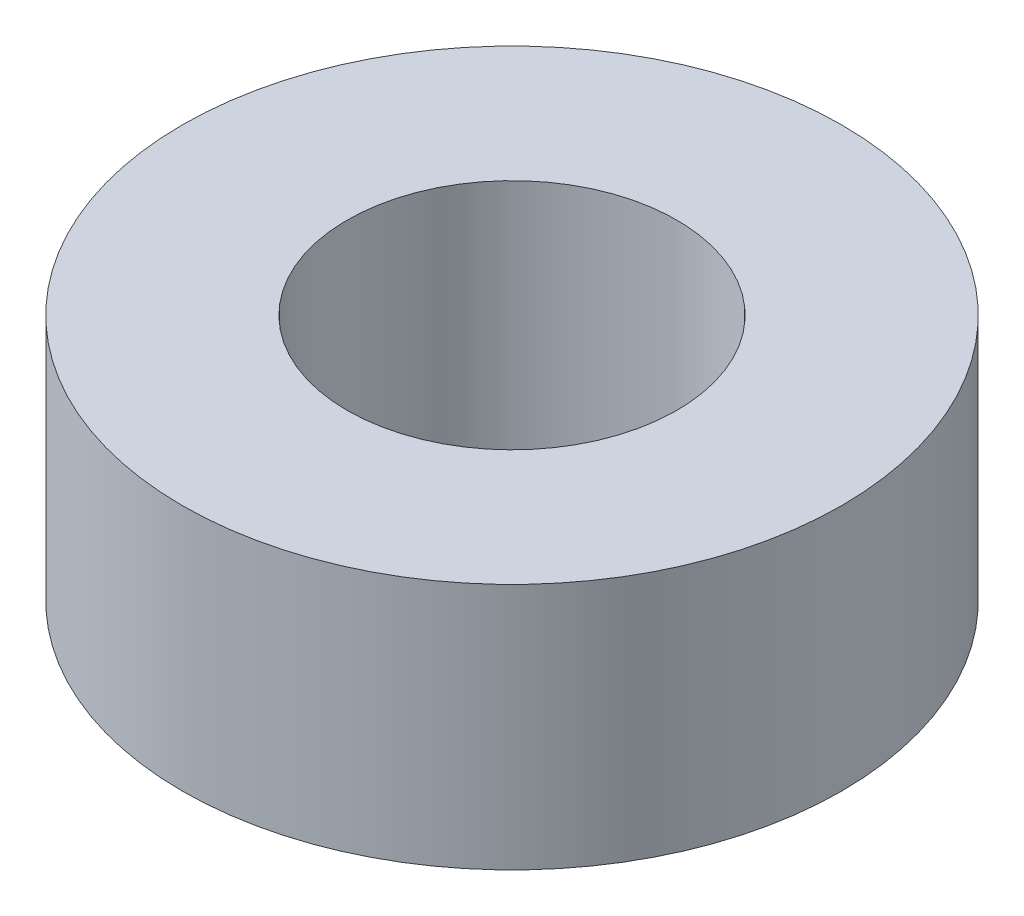
SolidWorks part; units mm, degrees
material "Commercially Pure CP-Ti UNS R50700  Grade 4 (SS)"
ref_plane "Front Plane" through (0, 0, 0) normal (0, 0, 1) x (1, 0, 0)
ref_plane "Top Plane" through (0, 0, 0) normal (0, 1, 0) x (1, 0, 0)
ref_plane "Right Plane" through (0, 0, 0) normal (1, 0, 0) x (0, 0, -1)
other "Bounding Box"
ref_plane "Default Plane" through (-8.9266, -12.7485, 0) normal (-0.1736, 0.9848, 0) x (0.9848, 0.1736, 0)
sketch "Sketch1" plane through (0, 0, 0) normal (0, 1, 0) x (1, 0, 0)
  circle A0 centre (0, 0) radius 3.175
  circle A1 centre (0, 0) radius 6.35
  dimension "D1" = 6.35
  dimension "D2" = 12.7
extrude "Boss-Extrude1" add sketch "Sketch1" along normal blind 4.7625
